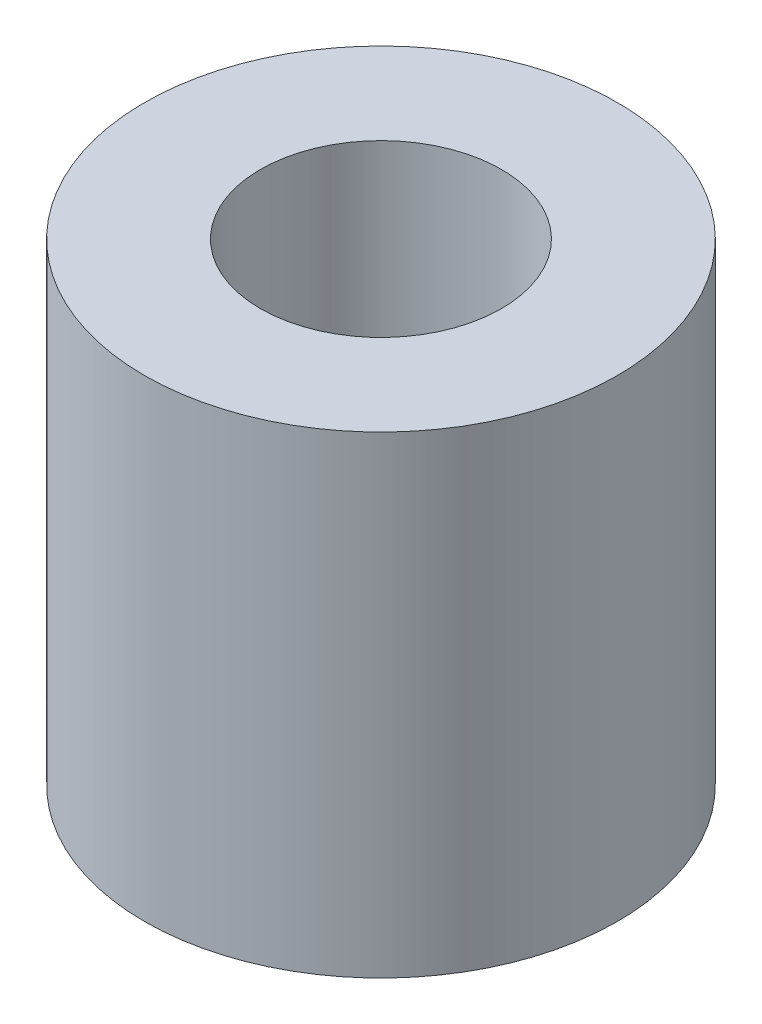
SolidWorks part; units mm, degrees
ref_plane "Ebene vorne" through (0, 0, 0) normal (0, 0, 1) x (1, 0, 0)
ref_plane "Ebene oben" through (0, 0, 0) normal (0, 1, 0) x (1, 0, 0)
ref_plane "Ebene rechts" through (0, 0, 0) normal (1, 0, 0) x (0, 0, -1)
sketch "Skizze1" plane through (0, 0, 0) normal (0, 1, 0) x (1, 0, 0)
  circle A0 centre (0, 0) radius 10
  dimension "D1" = 20
extrude "Zapfen" add sketch "Skizze1" along normal blind 20
hole_wizard "M12 Gewindebohrung1" positions "Skizze2" profile "Skizze3" tap size "M12" standard "DIN"
sketch "Skizze2" plane through (0, 20, 0) normal (0, 1, 0) x (1, 0, 0)
  point P0 (0, 0)
sketch "Skizze3" plane through (0, 20, 0) normal (1, 0, 0) x (0, 0, 1)
  line L0 (0, 0) -> (0, 19.0644)
  line L1 (0, 19.0644) -> (5.1, 16)
  line L2 (5.1, 16) -> (5.1, 0)
  line L5 (5.1, 0) -> (0, 0)
  line L10 (0, 19.0644) -> (-5.1, 16) construction
  line L11 (0, -6.35) -> (0, 107.95) construction
  dimension "Bohrerdurchmesser" = 10.2
  dimension "Bohrungstiefe" = 16
  dimension "Spitzenwinkel" = 118
cosmetic thread "Bohrungsgewinde1" parameters "D1"=16, "D2"=12
